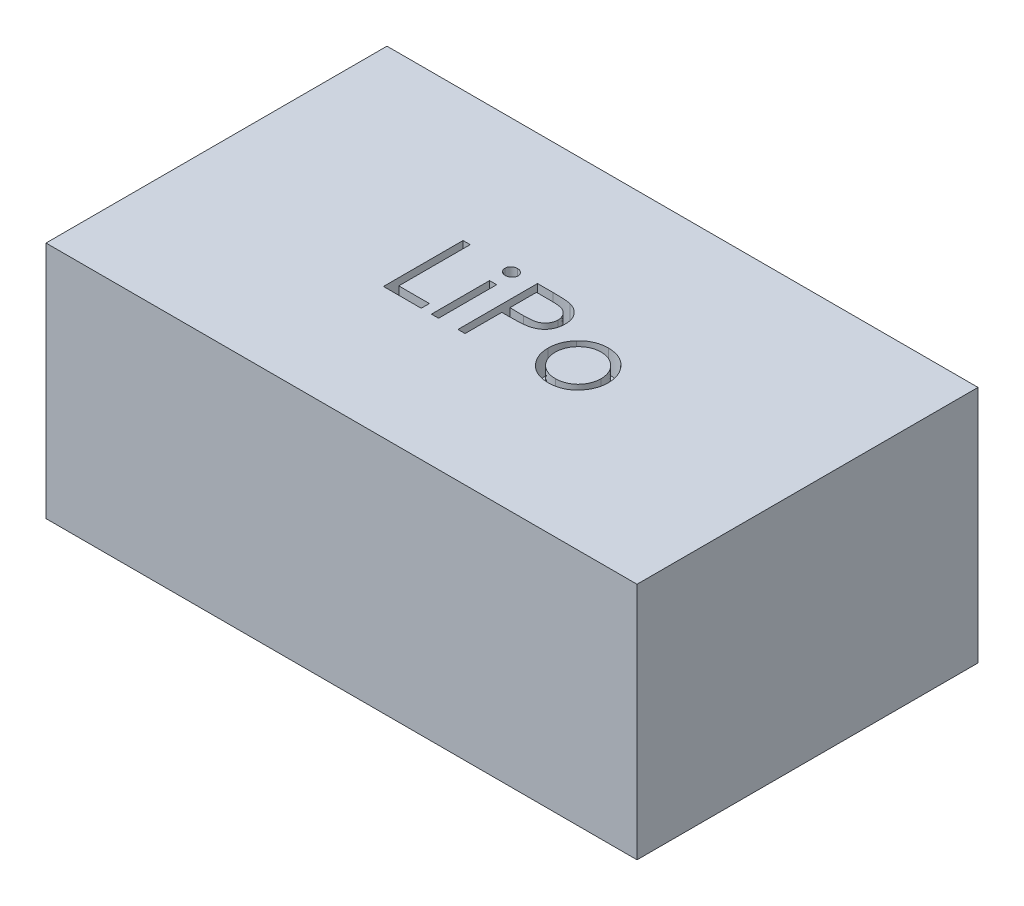
SolidWorks part; units mm, degrees
ref_plane "Front Plane" through (0, 0, 0) normal (0, 0, 1) x (1, 0, 0)
ref_plane "Top Plane" through (0, 0, 0) normal (0, 1, 0) x (1, 0, 0)
ref_plane "Right Plane" through (0, 0, 0) normal (1, 0, 0) x (0, 0, -1)
sketch "Sketch1" plane through (0, 0, 0) normal (0, 1, 0) x (1, 0, 0)
  line L0 (0, 15) -> (0, -15) construction
  line L1 (-26, 15) -> (26, 15)
  line L2 (-26, 15) -> (-26, -15)
  line L3 (-26, -15) -> (26, -15)
  line L4 (26, 15) -> (26, -15)
  dimension "D1" = 52
  dimension "D2" = 30
extrude "Boss-Extrude1" add sketch "Sketch1" along normal blind 21
sketch "Sketch2" plane through (0, 21, 0) normal (0, 1, 0) x (1, 0, 0)
  text T0 "LiPo" font "Century Gothic" height 7
extrude "Cut-Extrude1" cut sketch "Sketch2" against normal blind 2
